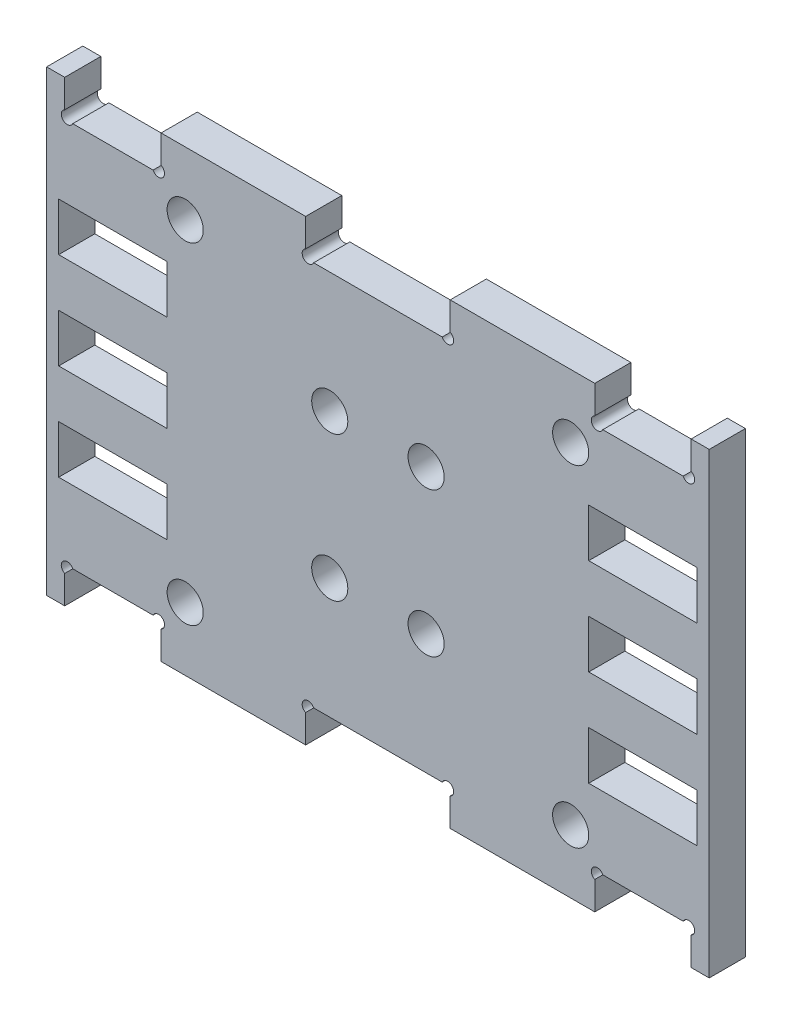
SolidWorks part; units mm, degrees
ref_plane "前视基准面" through (0, 0, 0) normal (0, 0, 1) x (1, 0, 0)
ref_plane "上视基准面" through (0, 0, 0) normal (0, 1, 0) x (1, 0, 0)
ref_plane "右视基准面" through (0, 0, 0) normal (1, 0, 0) x (0, 0, -1)
sketch "草图1" plane through (0, 0, 0) normal (0, 0, 1) x (1, 0, 0)
  line L1 (-27.5, 19) -> (27.5, 19)
  line L2 (-27.5, 19) -> (-27.5, -19)
  line L3 (-27.5, -19) -> (27.5, -19)
  line L4 (27.5, 19) -> (27.5, -19)
  line L5 (-27.5, 19) -> (27.5, -19) construction
  line L6 (-27.5, -19) -> (27.5, 19) construction
  point P0 (0, 0)
  dimension "D1" = 38
  dimension "D2" = 55
extrude "凸台-拉伸1" add sketch "草图1" along normal blind 3
sketch "草图2" plane through (0, 0, 3) normal (0, 0, 1) x (1, 0, 0)
  line L0 (-34.5256, 0) -> (42.1415, 0) construction
  line L1 (-10, -19) -> (-10, 19) construction
  line L2 (-27.5, -19) -> (27.5, -19) construction
  line L3 (27.5, 19) -> (-27.5, 19) construction
  line L4 (0, 26.7268) -> (0, -34.771) construction
  line L5 (10, -19) -> (10, 19) construction
  circle A0 centre (16, 13.75) radius 1.5
  circle A1 centre (16, -13.75) radius 1.5
  circle A2 centre (-16, 13.75) radius 1.5
  circle A3 centre (-16, -13.75) radius 1.5
  dimension "D1" = 13.75
  dimension "D2" = 3
  dimension "D3" = 10
  dimension "D4" = 6
extrude "切除-拉伸1" cut sketch "草图2" against normal blind 30
sketch "草图3" plane through (0, 0, 3) normal (0, 0, 1) x (1, 0, 0)
  line L0 (10, -19) -> (10, 19) construction
  line L1 (0, 26.7268) -> (0, -34.771) construction
  line L2 (-34.5256, 0) -> (42.1415, 0) construction
  line L3 (-10, -19) -> (-10, 19) construction
  line L4 (10, -19) -> (10, 19) construction
  line L5 (0, 26.7268) -> (0, -34.771) construction
  line L6 (-34.5256, 0) -> (42.1415, 0) construction
  line L7 (-10, -19) -> (-10, 19) construction
  line L8 (27.5, 19) -> (-27.5, 19) construction
  line L9 (27.5, -19) -> (27.5, 19) construction
  line L12 (18, 19) -> (26, 19)
  line L13 (18, 19) -> (18, 16)
  line L14 (18, 16) -> (26, 16)
  line L15 (26, 19) -> (26, 16)
  line L17 (26, -19) -> (26, -16)
  line L18 (18, -16) -> (26, -16)
  line L19 (18, -19) -> (18, -16)
  line L20 (18, -19) -> (26, -19)
  line L21 (-26, 19) -> (-26, 16)
  line L22 (-18, 16) -> (-26, 16)
  line L23 (-18, 19) -> (-18, 16)
  line L24 (-18, 19) -> (-26, 19)
  line L25 (-18, -19) -> (-26, -19)
  line L26 (-18, -19) -> (-18, -16)
  line L27 (-18, -16) -> (-26, -16)
  line L28 (-26, -19) -> (-26, -16)
  circle A0 centre (16, 13.75) radius 4 construction
  dimension "D1" = 8
  dimension "D2" = 1.5
  dimension "D3" = 8
  dimension "D4" = 3
extrude "切除-拉伸2" cut sketch "草图3" against normal blind 30
sketch "草图4" plane through (0, 0, 3) normal (0, 0, 1) x (1, 0, 0)
  line L0 (10, -19) -> (10, 19) construction
  line L1 (-10, -19) -> (-10, 19) construction
  line L2 (10, -19) -> (10, 19)
  line L3 (-10, -19) -> (-10, 19)
  line L4 (-10, -19) -> (10, -19)
  line L5 (-10, 19) -> (10, 19)
extrude "切除-拉伸3" [suppressed] cut sketch "草图4" against normal blind 1
sketch "草图5" plane through (0, 0, 3) normal (0, 0, 1) x (1, 0, 0)
  line L0 (-18, -19) -> (18, -19) construction
  line L1 (6, -19) -> (-6, -19)
  line L2 (6, -19) -> (6, -16)
  line L3 (6, -16) -> (-6, -16)
  line L4 (-6, -19) -> (-6, -16)
  line L5 (6, -19) -> (-6, -16) construction
  line L6 (6, -16) -> (-6, -19) construction
  line L7 (34.427, 0) -> (-42.806, 0) construction
  line L8 (6, 16) -> (-6, 19) construction
  line L9 (6, 19) -> (-6, 16) construction
  line L10 (-6, 19) -> (-6, 16)
  line L11 (6, 16) -> (-6, 16)
  line L12 (6, 19) -> (6, 16)
  line L13 (6, 19) -> (-6, 19)
  point P0 (0, -17.5)
  point P14 (0, 17.5)
  dimension "D1" = 3
  dimension "D2" = 12
extrude "切除-拉伸4" cut sketch "草图5" against normal blind 10
sketch "草图6" plane through (0, 0, 0) normal (0, 0, -1) x (-1, 0, 0)
  line L0 (-17.5, -6) -> (-17.5, -10) construction
  line L1 (-17.5, -10) -> (-26.5, -10) construction
  line L2 (-26.5, -10) -> (-26.5, -6) construction
  line L3 (-26.5, -6) -> (-17.5, -6) construction
  line L4 (-17.5, 2) -> (-17.5, -2) construction
  line L5 (-17.5, -2) -> (-26.5, -2) construction
  line L6 (-26.5, -2) -> (-26.5, 2) construction
  line L7 (-26.5, 2) -> (-17.5, 2) construction
  line L8 (-17.5, 10) -> (-17.5, 6) construction
  line L9 (-17.5, 6) -> (-26.5, 6) construction
  line L10 (-26.5, 6) -> (-26.5, 10) construction
  line L11 (-26.5, 10) -> (-17.5, 10) construction
  line L12 (26.5, -6) -> (26.5, -10) construction
  line L13 (26.5, -10) -> (17.5, -10) construction
  line L14 (17.5, -10) -> (17.5, -6) construction
  line L15 (17.5, -6) -> (26.5, -6) construction
  line L16 (26.5, 2) -> (26.5, -2) construction
  line L17 (26.5, -2) -> (17.5, -2) construction
  line L18 (17.5, -2) -> (17.5, 2) construction
  line L19 (17.5, 2) -> (26.5, 2) construction
  line L20 (17.5, 6) -> (17.5, 10) construction
  line L21 (26.5, 6) -> (17.5, 6) construction
  line L22 (26.5, 10) -> (26.5, 6) construction
  line L23 (17.5, 10) -> (26.5, 10) construction
  line L24 (-17.5, -6) -> (-17.5, -10)
  line L25 (-17.5, -10) -> (-26.5, -10)
  line L26 (-26.5, -10) -> (-26.5, -6)
  line L27 (-26.5, -6) -> (-17.5, -6)
  line L28 (-17.5, 2) -> (-17.5, -2)
  line L29 (-17.5, -2) -> (-26.5, -2)
  line L30 (-26.5, -2) -> (-26.5, 2)
  line L31 (-26.5, 2) -> (-17.5, 2)
  line L32 (-17.5, 10) -> (-17.5, 6)
  line L33 (-17.5, 6) -> (-26.5, 6)
  line L34 (-26.5, 6) -> (-26.5, 10)
  line L35 (-26.5, 10) -> (-17.5, 10)
  line L36 (26.5, -6) -> (26.5, -10)
  line L37 (26.5, -10) -> (17.5, -10)
  line L38 (17.5, -10) -> (17.5, -6)
  line L39 (17.5, -6) -> (26.5, -6)
  line L40 (26.5, 2) -> (26.5, -2)
  line L41 (26.5, -2) -> (17.5, -2)
  line L42 (17.5, -2) -> (17.5, 2)
  line L43 (17.5, 2) -> (26.5, 2)
  line L44 (17.5, 6) -> (17.5, 10)
  line L45 (26.5, 6) -> (17.5, 6)
  line L46 (26.5, 10) -> (26.5, 6)
  line L47 (17.5, 10) -> (26.5, 10)
extrude "切除-拉伸5" cut sketch "草图6" against normal blind 10
sketch "草图7" plane through (0, 0, 0) normal (0, 0, -1) x (-1, 0, 0)
  circle A1 centre (-18.2121, -16.2121) radius 0.5
  circle A2 centre (-18.2121, -16.2121) radius 0.5
  circle A3 centre (-25.7879, -16.2121) radius 0.5
  circle A4 centre (-25.7879, -16.2121) radius 0.5
  circle A5 centre (-25.7879, 16.2121) radius 0.5
  circle A6 centre (-25.7879, 16.2121) radius 0.5
  circle A7 centre (-18.2121, 16.2121) radius 0.5
  circle A8 centre (-18.2121, 16.2121) radius 0.5
  circle A9 centre (-5.7879, -16.2121) radius 0.5
  circle A10 centre (-5.7879, -16.2121) radius 0.5
  circle A11 centre (25.7879, -16.2121) radius 0.5
  circle A12 centre (25.7879, -16.2121) radius 0.5
  circle A13 centre (18.2121, -16.2121) radius 0.5
  circle A14 centre (18.2121, -16.2121) radius 0.5
  circle A15 centre (18.2121, 16.2121) radius 0.5
  circle A16 centre (18.2121, 16.2121) radius 0.5
  circle A17 centre (25.7879, 16.2121) radius 0.5
  circle A18 centre (25.7879, 16.2121) radius 0.5
  circle A19 centre (-5.7879, 16.2121) radius 0.5
  circle A20 centre (-5.7879, 16.2121) radius 0.5
  circle A21 centre (5.7879, 16.2121) radius 0.5
  circle A22 centre (5.7879, 16.2121) radius 0.5
  circle A23 centre (5.7879, -16.2121) radius 0.5
  circle A24 centre (5.7879, -16.2121) radius 0.5
  dimension "D1" = 0
  dimension "D2" = 0
  dimension "D3" = 0
  dimension "D4" = 0
  dimension "D5" = 0
  dimension "D6" = 0
  dimension "D7" = 0
  dimension "D8" = 0
  dimension "D9" = 0
  dimension "D10" = 0
  dimension "D11" = 0
  dimension "D12" = 0
extrude "切除-拉伸6" cut sketch "草图7" against normal blind 10
sketch "草图8" plane through (0, 0, 0) normal (0, 0, -1) x (-1, 0, 0)
  line L0 (-7.0641, 0) -> (9.3517, 0)
  line L1 (9.3517, 0) -> (0, 0)
  line L2 (0, 0) -> (0, 12.297)
  line L4 (-4, 6) -> (4, 6)
  line L5 (-4, 6) -> (-4, -6)
  line L6 (-4, -6) -> (4, -6)
  line L7 (4, 6) -> (4, -6)
  circle A0 centre (-4, 6) radius 1.5
  circle A1 centre (-4, -6) radius 1.5
  circle A2 centre (4, -6) radius 1.5
  circle A3 centre (4, 6) radius 1.5
  dimension "D5" = 3
  dimension "D6" = 3
  dimension "D7" = 3
  dimension "D8" = 3
  dimension "D1" = 12
  dimension "D2" = 8
  dimension "D3" = 4
  dimension "D4" = 6
extrude "切除-拉伸7" cut sketch "草图8" against normal blind 20 contours L5 A0 L4 | L4 A0 L5 | L4 A3 L7 | L7 A3 L4 | L7 A2 L6 | L6 A2 L7 | L6 A1 L5 | L5 A1 L6
